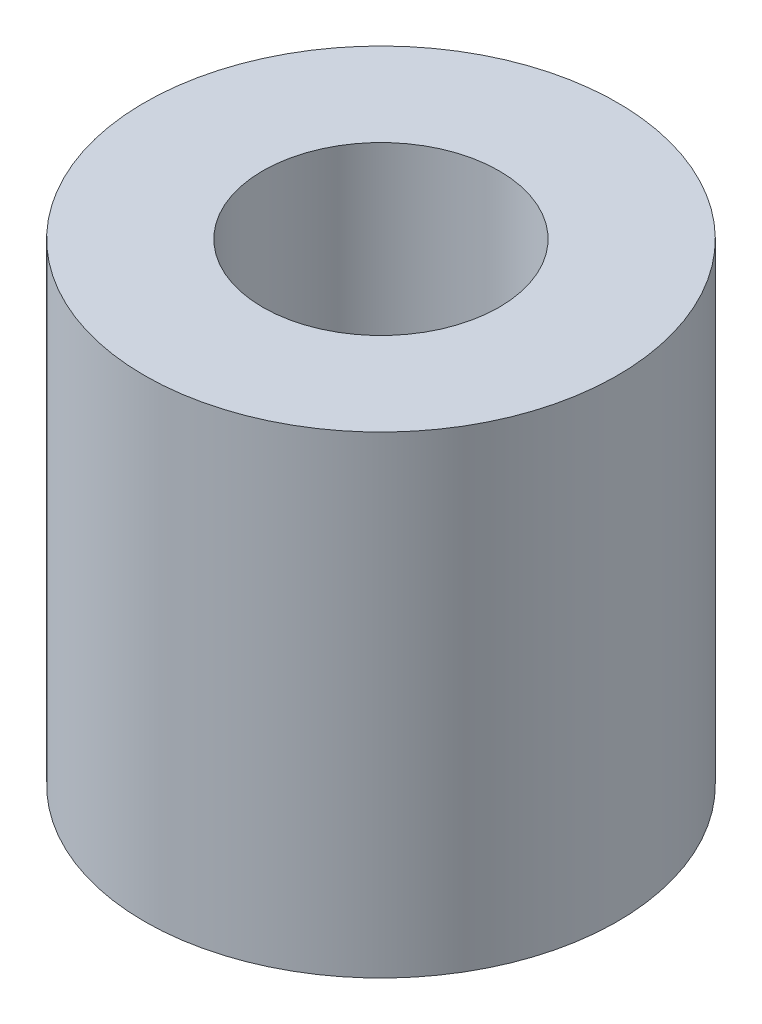
SolidWorks part; units mm, degrees
ref_plane "Front Plane" through (0, 0, 0) normal (0, 0, 1) x (1, 0, 0)
ref_plane "Top Plane" through (0, 0, 0) normal (0, 1, 0) x (1, 0, 0)
ref_plane "Right Plane" through (0, 0, 0) normal (1, 0, 0) x (0, 0, -1)
sketch "Sketch1" plane through (0, 0, 0) normal (0, 1, 0) x (1, 0, 0)
  circle A0 centre (0, 0) radius 3.175
  circle A1 centre (0, 0) radius 6.35
  dimension "D1" = 6.35
  dimension "D2" = 12.7
extrude "Boss-Extrude1" add sketch "Sketch1" along normal blind 12.7
